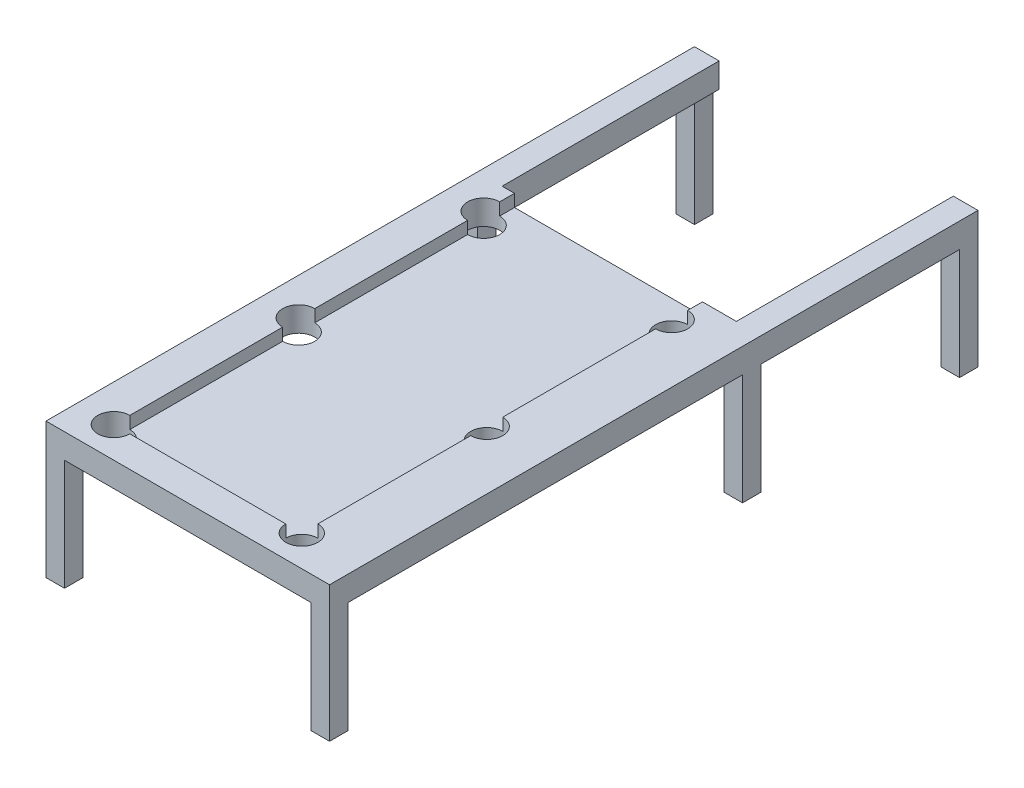
SolidWorks part; units mm, degrees
ref_plane "Front Plane" through (0, 0, 0) normal (0, 0, 1) x (1, 0, 0)
ref_plane "Top Plane" through (0, 0, 0) normal (0, 1, 0) x (1, 0, 0)
ref_plane "Right Plane" through (0, 0, 0) normal (1, 0, 0) x (0, 0, -1)
sketch "Sketch2" plane through (0, 0, 0) normal (0, 1, 0) x (1, 0, 0)
  line L1 (0, 0) -> (460, 0)
  line L2 (0, 0) -> (0, 700)
  line L3 (0, 700) -> (460, 700)
  line L4 (460, 0) -> (460, 700)
  line L5 (60, 50) -> (365, 50)
  line L6 (60, 50) -> (60, 650)
  line L7 (60, 650) -> (365, 650)
  line L8 (365, 50) -> (365, 650)
  dimension "D1" = 700
  dimension "D2" = 460
  dimension "D3" = 600
  dimension "D4" = 305
  dimension "D5" = 60
  dimension "D6" = 50
extrude "Boss-Extrude1" add sketch "Sketch2" along normal blind 20
ref_plane "Plane1" through (0, 0, -700) normal (0, 0, -1) x (-1, 0, 0)
sketch "Sketch10" plane through (0, 0, 0) normal (0, -1, 0) x (1, 0, 0)
  line L1 (0, 0) -> (460, 0)
  line L2 (0, 0) -> (0, -700)
  line L3 (0, -700) -> (460, -700)
  line L4 (460, 0) -> (460, -700)
extrude "Boss-Extrude6" add sketch "Sketch10" along normal blind 20
sketch "Sketch11" plane through (0, -20, 0) normal (0, -1, 0) x (1, 0, 0)
  line L1 (0, 0) -> (30, 0)
  line L2 (0, 0) -> (0, -30)
  line L3 (0, -30) -> (30, -30)
  line L4 (30, 0) -> (30, -30)
  line L5 (460, 0) -> (430, 0)
  line L6 (460, 0) -> (460, -30)
  line L7 (460, -30) -> (430, -30)
  line L8 (430, 0) -> (430, -30)
  line L9 (0, -700) -> (30, -700)
  line L10 (0, -700) -> (0, -670)
  line L11 (0, -670) -> (30, -670)
  line L12 (30, -700) -> (30, -670)
  line L13 (460, -700) -> (430, -700)
  line L14 (460, -700) -> (460, -670)
  line L15 (460, -670) -> (430, -670)
  line L16 (430, -700) -> (430, -670)
  dimension "D1" = 30
extrude "Boss-Extrude7" add sketch "Sketch11" along normal blind 180
sketch "Sketch14" plane through (0, 20, 0) normal (0, 1, 0) x (1, 0, 0)
  line L0 (121, 700) -> (-121, 700) construction
  line L1 (0, 700) -> (40, 700)
  line L2 (0, 700) -> (0, 1052)
  line L3 (0, 1052) -> (40, 1052)
  line L4 (40, 700) -> (40, 1052)
  line L5 (0, 700) -> (0, 0) construction
  line L6 (460, 0) -> (460, 700) construction
  line L7 (460, 700) -> (420, 700)
  line L8 (460, 700) -> (460, 1052)
  line L9 (460, 1052) -> (420, 1052)
  line L10 (420, 700) -> (420, 1052)
  dimension "D3" = 40
  dimension "D4" = 40
extrude "Boss-Extrude8" add sketch "Sketch14" against normal blind 40
sketch "Sketch15" plane through (0, -20, 0) normal (0, -1, 0) x (1, 0, 0)
  line L1 (460, -1052) -> (430, -1052)
  line L2 (460, -1052) -> (460, -1022)
  line L3 (460, -1022) -> (430, -1022)
  line L4 (430, -1052) -> (430, -1022)
  line L6 (0, -1052) -> (30, -1052)
  line L7 (0, -1052) -> (0, -1022)
  line L8 (0, -1022) -> (30, -1022)
  line L9 (30, -1052) -> (30, -1022)
  dimension "D1" = 30
  dimension "D2" = 30
  dimension "D3" = 30
  dimension "D4" = 30
extrude "Boss-Extrude9" add sketch "Sketch15" along normal blind 180
sketch "Sketch17" plane through (0, 20, 0) normal (0, 1, 0) x (1, 0, 0)
  line L0 (60, 650) -> (60, 50) construction
  line L1 (365, 50) -> (365, 650) construction
  circle A0 centre (60, 650) radius 26
  circle A1 centre (60, 350) radius 26
  circle A2 centre (60, 50) radius 26
  circle A3 centre (365, 50) radius 26
  circle A4 centre (365, 350) radius 26
  circle A5 centre (365, 650) radius 26
  line M15 (60, 50) -> (60, 650)
  line M16 (60, 650) -> (365, 650)
  line M17 (365, 650) -> (365, 50)
  line M18 (365, 50) -> (60, 50)
  dimension "D1" = 52
extrude "Cut-Extrude1" cut sketch "Sketch17" against normal blind 60 contours A5 M17 M16 | A4 M17 | A3 M18 M17 | A1 M15 | A1 M15 | A2 M15 M18 | A2 M18 M15 | A3 M17 M18 | A5 M16 M17 | A4 M17 | A0
sketch "Sketch18" plane through (0, 20, 0) normal (0, 1, 0) x (1, 0, 0)
  line L1 (60, 700) -> (365, 700)
  line L9 (339, 650) -> (86, 650) construction
  line L10 (420, 700) -> (40, 700) construction
  line L12 (365, 700) -> (365, 650)
  line L14 (212.5, 650) -> (365, 650)
  line L16 (60, 700) -> (60, 650)
  line L17 (60, 650) -> (212.5, 650)
  arc A0 (86, 650) -> (60, 624) centre (60, 650) ccw construction
  arc A1 (365, 624) -> (339, 650) centre (365, 650) ccw construction
extrude "Cut-Extrude2" cut sketch "Sketch18" against normal blind 20
